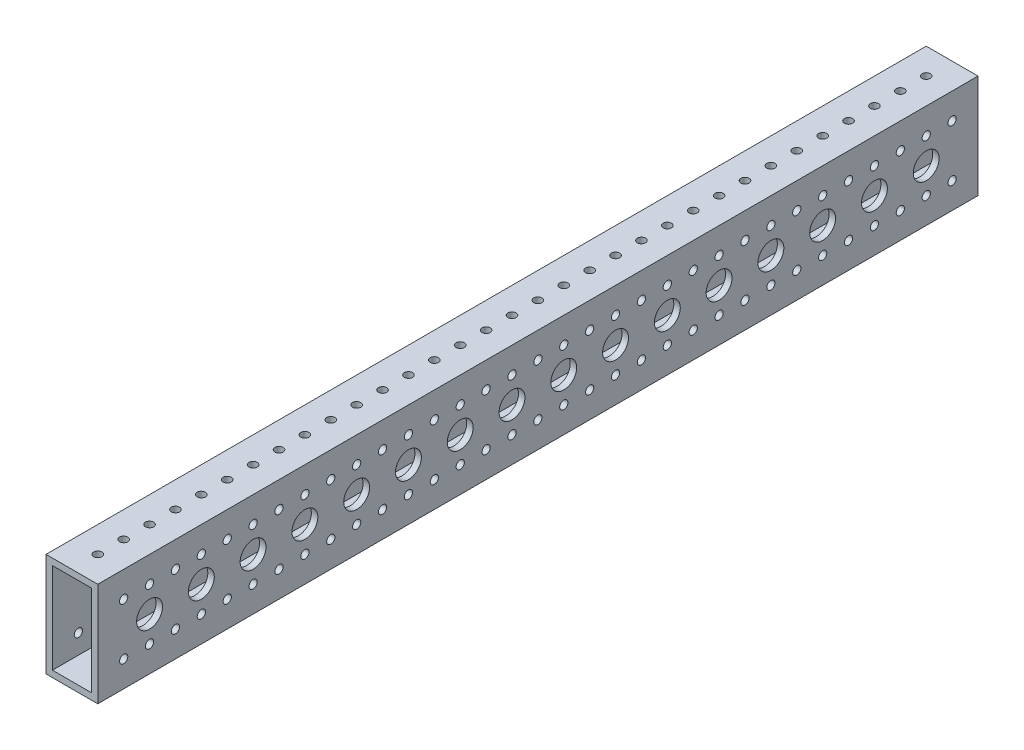
SolidWorks part; units mm, degrees
material "6061 Alloy"
ref_plane "Front Plane" through (0, 0, 0) normal (0, 0, 1) x (1, 0, 0)
ref_plane "Top Plane" through (0, 0, 0) normal (0, 1, 0) x (1, 0, 0)
ref_plane "Right Plane" through (0, 0, 0) normal (1, 0, 0) x (0, 0, -1)
sketch "Sketch1" plane through (0, 0, 0) normal (0, 0, 1) x (1, 0, 0)
  line L0 (-9.525, 22.225) -> (9.525, 22.225)
  line L1 (-12.7, 25.4) -> (12.7, 25.4)
  line L2 (-12.7, 25.4) -> (-12.7, -25.4)
  line L3 (-12.7, -25.4) -> (12.7, -25.4)
  line L4 (12.7, 25.4) -> (12.7, -25.4)
  line L5 (-12.7, 25.4) -> (12.7, -25.4) construction
  line L6 (-12.7, -25.4) -> (12.7, 25.4) construction
  line L7 (9.525, 22.225) -> (9.525, -22.225)
  line L8 (-9.525, -22.225) -> (9.525, -22.225)
  line L9 (-9.525, 22.225) -> (-9.525, -22.225)
  point P0 (0, 0)
  dimension "D1" = 50.8
  dimension "D2" = 25.4
  dimension "D3" = 3.175
extrude "Boss-Extrude1" add sketch "Sketch1" along normal blind 431.8
sketch "Sketch7" plane through (-12.7, 0, 0) normal (-1, 0, 0) x (0, 0, 1)
  line L0 (431.8, 25.4) -> (0, 25.4) construction
  line L1 (0, 25.4) -> (0, -25.4) construction
  point P0 (25.4, 0)
  dimension "D1" = 25.4
  dimension "D2" = 25.4
hole_wizard "1/2 (0.5) Diameter Hole1" positions "Sketch8" profile "Sketch9" hole size "1/2" standard "ANSI Inch" end condition through all
sketch "Sketch8" plane through (-12.7, 0, 0) normal (-1, 0, 0) x (0, 0, 1)
  point P0 (25.4, 0)
sketch "Sketch9" plane through (-12.7, 0, 25.4) normal (0, 1, 0) x (0, 0, 1)
  line L0 (0, 0) -> (0, 25.4)
  line L1 (0, 25.4) -> (6.35, 25.4)
  line L2 (6.35, 25.4) -> (6.35, 0)
  line L5 (6.35, 0) -> (0, 0)
  line L11 (0, -6.35) -> (0, 107.95) construction
  dimension "Thru Hole Dia." = 12.7
  dimension "Thru Hole Depth" = 25.4
pattern_linear "LPattern1" count 16 spacing 25.4 along (0, 0, 1) of "1/2 (0.5) Diameter Hole1"
sketch "Sketch10" plane through (-12.7, 0, 0) normal (-1, 0, 0) x (0, 0, 1)
  line L0 (431.8, 25.4) -> (0, 25.4) construction
  line L1 (0, 25.4) -> (0, -25.4) construction
  point P0 (12.7, 12.7)
  dimension "D1" = 12.7
  dimension "D2" = 12.7
hole_wizard "#21 (0.159) Diameter Hole1" positions "Sketch11" profile "Sketch12" hole size "#21" standard "ANSI Inch" end condition through all
sketch "Sketch11" plane through (-12.7, 0, 0) normal (-1, 0, 0) x (0, 0, 1)
  point P0 (12.7, 12.7)
sketch "Sketch12" plane through (-12.7, 12.7, 12.7) normal (0, 1, 0) x (0, 0, 1)
  line L0 (0, 0) -> (0, 25.4)
  line L1 (0, 25.4) -> (2.0193, 25.4)
  line L2 (2.0193, 25.4) -> (2.0193, 0)
  line L5 (2.0193, 0) -> (0, 0)
  line L11 (0, -6.35) -> (0, 107.95) construction
  dimension "Thru Hole Dia." = 4.0386
  dimension "Thru Hole Depth" = 25.4
pattern_linear "LPattern2" count 33 spacing 12.7 along (0, 0, 1) count 2 spacing 25.4 along (0, -1, 0) of "#21 (0.159) Diameter Hole1"
sketch "Sketch13" plane through (0, 25.4, 0) normal (0, 1, 0) x (1, 0, 0)
  line L0 (12.7, -431.8) -> (12.7, 0) construction
  line L1 (12.7, 0) -> (-12.7, 0) construction
  point P0 (0, -12.7)
  dimension "D1" = 12.7
  dimension "D2" = 12.7
hole_wizard "#21 (0.159) Diameter Hole2" positions "Sketch14" profile "Sketch15" hole size "#21" standard "ANSI Inch" end condition through all
sketch "Sketch14" plane through (0, 25.4, 0) normal (0, 1, 0) x (1, 0, 0)
  point P0 (0, -12.7)
sketch "Sketch15" plane through (0, 25.4, 12.7) normal (1, 0, 0) x (0, 0, 1)
  line L0 (0, 0) -> (0, 50.8)
  line L1 (0, 50.8) -> (2.0193, 50.8)
  line L2 (2.0193, 50.8) -> (2.0193, 0)
  line L5 (2.0193, 0) -> (0, 0)
  line L11 (0, -6.35) -> (0, 107.95) construction
  dimension "Thru Hole Dia." = 4.0386
  dimension "Thru Hole Depth" = 50.8
pattern_linear "LPattern3" count 33 spacing 12.7 along (0, 0, 1) of "#21 (0.159) Diameter Hole2"
sketch "Sketch16" [suppressed] plane through (12.7, 0, 0) normal (1, 0, 0) x (0, 0, -1)
  line L0 (0, -25.4) -> (0, 25.4) construction
  circle A0 centre (-101.6, 0) radius 14.2875
  dimension "D1" = 28.575
  dimension "D2" = 101.6
extrude "Cut-Extrude1" [suppressed] cut sketch "Sketch16" against normal through all both and the other way through all
equation "\"raptorlength\"= \"length@Drivetrain-1.Assembly\""
equation "\"D1@Boss-Extrude1\"     = \"raptorlength\""
equation "\"other length\"= \"raptorlength\" - 2"
equation "\"shorterlength\"= \"shorter@Drivetrain-1.Assembly\""
equation "\"hi\"= \"structure@Drivetrain-1.Assembly\""
